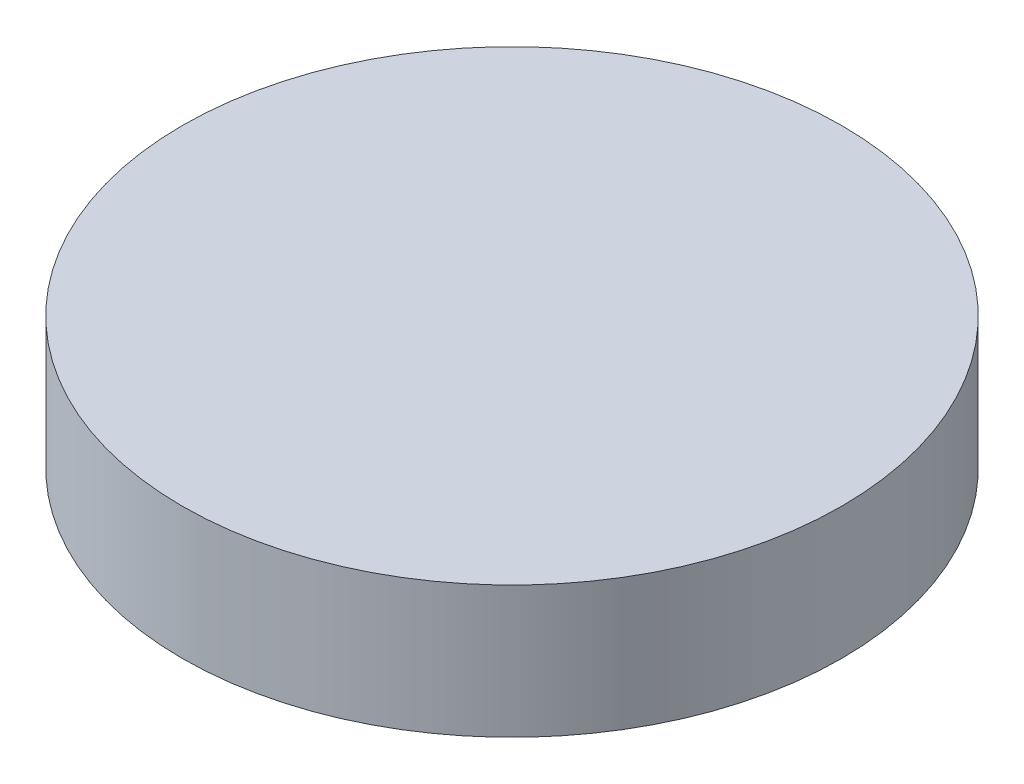
SolidWorks part; units mm, degrees
ref_plane "Front" through (0, 0, 0) normal (0, 0, 1) x (1, 0, 0)
ref_plane "Top" through (0, 0, 0) normal (0, 1, 0) x (1, 0, 0)
ref_plane "Right" through (0, 0, 0) normal (1, 0, 0) x (0, 0, -1)
sketch "Sketch1" plane through (0, 0, 0) normal (0, 1, 0) x (1, 0, 0)
  circle A0 centre (0, 0) radius 31.75
  dimension "D1" = 63.5
extrude "Boss-Extrude1" add sketch "Sketch1" along normal blind 12.7
sketch "Sketch2" plane through (0, 0, 0) normal (0, -1, 0) x (1, 0, 0)
  circle A0 centre (0, 0) radius 5.588
  dimension "D1" = 11.176
extrude "Boss-Extrude2" add sketch "Sketch2" along normal blind 12.7
